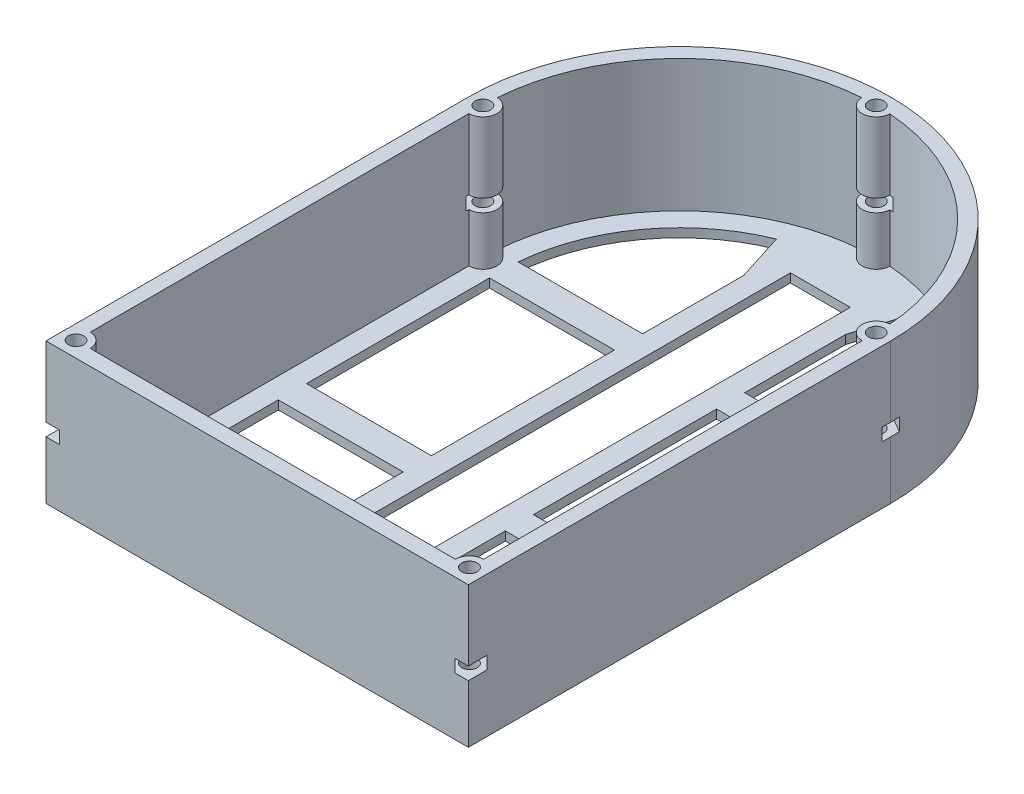
SolidWorks part; units mm, degrees
ref_plane "Front Plane" through (0, 0, 0) normal (0, 0, 1) x (1, 0, 0)
ref_plane "Top Plane" through (0, 0, 0) normal (0, 1, 0) x (1, 0, 0)
ref_plane "Right Plane" through (0, 0, 0) normal (1, 0, 0) x (0, 0, -1)
sketch "Sketch1" plane through (0, 0, 0) normal (0, 1, 0) x (1, 0, 0)
  line L1 (-30, 0) -> (30, 0) construction
  line L2 (-30, 0) -> (-30, -60)
  line L3 (-30, -60) -> (30, -60)
  line L4 (30, 0) -> (30, -60)
  line L5 (-30, 0) -> (30, -60) construction
  line L6 (-30, -60) -> (30, 0) construction
  line L9 (27.785, -57.785) -> (27.94, -57.785)
  line L10 (27.94, -55.785) -> (27.94, -2)
  line L11 (-25.94, -57.785) -> (25.94, -57.785)
  line L12 (-27.94, -2) -> (-27.94, -55.785)
  arc A0 (-30, 0) -> (30, 0) centre (0, 0) cw
  circle A1 centre (27.94, 0) radius 1.1
  circle A2 centre (-27.94, 0) radius 1.1
  circle A3 centre (0, 27.94) radius 1.1
  circle A4 centre (-27.94, -57.785) radius 1.1
  circle A5 centre (27.94, -57.785) radius 1.1
  arc A7 (27.8684, 1.9987) -> (27.94, -2) centre (27.94, 0) ccw
  arc A8 (27.94, -55.785) -> (25.94, -57.785) centre (27.94, -57.785) ccw
  arc A9 (-25.94, -57.785) -> (-27.94, -55.785) centre (-27.94, -57.785) ccw
  arc A11 (-1.9987, 27.8684) -> (1.9987, 27.8684) centre (0, 27.94) ccw
  circle A12 centre (0, 27.94) radius 2 construction
  circle A13 centre (27.94, 0) radius 2 construction
  arc A14 (1.9987, 27.8684) -> (27.8684, 1.9987) centre (0, 0) cw
  arc A15 (29.9391, -0.0609) -> (29.94, 0) centre (27.94, 0) ccw
  circle A16 centre (27.94, -57.785) radius 2 construction
  circle A17 centre (-27.94, -57.785) radius 2 construction
  arc A18 (-27.8684, 1.9987) -> (-1.9987, 27.8684) centre (0, 0) cw
  arc A19 (-27.94, -2) -> (-27.8684, 1.9987) centre (-27.94, 0) ccw
  point P0 (0, -30)
  dimension "D3" = 27.94
  dimension "D4" = 2.2
  dimension "D1" = 60
  dimension "D2" = 60
  dimension "D5" = 27.94
  dimension "D6" = 27.94
  dimension "D7" = 57.785
  dimension "D8" = 0.9
extrude "Boss-Extrude1" add sketch "Sketch1" against normal blind 20
sketch "Sketch2" plane through (0, -20, 0) normal (0, -1, 0) x (1, 0, 0)
  line L0 (-7.25, 53) -> (-7.25, 32)
  line L1 (-4.25, 50) -> (4.25, 50)
  line L2 (-4.25, 50) -> (-4.25, -20)
  line L3 (30, 0) -> (30, 60)
  line L4 (30, 60) -> (-30, 60)
  line L5 (-30, 60) -> (-30, 0)
  line L6 (30, 0) -> (30, 60)
  line L7 (30, 60) -> (-30, 60)
  line L8 (-30, 60) -> (-30, 0)
  line L9 (-4.25, -20) -> (4.25, -20)
  line L10 (4.25, 50) -> (4.25, -20)
  line L11 (-4.25, 50) -> (4.25, -20) construction
  line L12 (-4.25, -20) -> (4.25, 50) construction
  line L13 (-5.153, -23) -> (5.153, -23) construction
  line L14 (7.25, 53) -> (7.25, 32)
  line L16 (0, 0) -> (-7.5159, -23.8435) construction
  line L17 (25, 2) -> (25, 28)
  line L18 (0, 0) -> (7.5159, -23.8435) construction
  line L19 (25, 55) -> (7.25, 55)
  line L20 (-25, 55) -> (-25, 32)
  line L22 (-7.25, 53) -> (-7.25, 55)
  line L23 (5.153, -23) -> (5.5843, -24.3683) construction
  line L24 (-5.153, -23) -> (-5.5843, -24.3683) construction
  line L25 (-7.25, 53) -> (-7.25, -23) construction
  line L26 (-7.25, -23) -> (7.25, -23) construction
  line L27 (7.25, 53) -> (7.25, -23) construction
  line L28 (0, -6.6526) -> (-5.6084, -24.4448) construction
  line L29 (0, -6.6526) -> (5.6084, -24.4448) construction
  line L30 (-7.25, -16.3474) -> (-9.3993, -23.1658)
  line L31 (7.25, 53) -> (7.25, 55)
  line L32 (7.25, -16.3474) -> (9.3993, -23.1658)
  line L34 (-7.25, 55) -> (-25, 55)
  line L35 (25, 55) -> (-25, 55) construction
  line L36 (-7.25, 53) -> (7.25, 53) construction
  line L37 (-25, 0) -> (-7.25, 0) construction
  line L38 (25, 0) -> (7.25, 0) construction
  line L39 (7.25, 30) -> (25, 30) construction
  line L40 (-7.25, 30) -> (-25, 30) construction
  line L41 (-24.9199, -2) -> (-7.25, -2)
  line L42 (25, 2) -> (7.25, 2)
  line L43 (-7.25, 32) -> (-25, 32)
  line L44 (7.25, 28) -> (25, 28)
  line L45 (-25, 2) -> (-7.25, 2)
  line L46 (24.9199, -2) -> (7.25, -2)
  line L47 (-7.25, 28) -> (-25, 28)
  line L48 (7.25, 32) -> (25, 32)
  line L49 (7.25, 2) -> (7.25, 0) construction
  line L50 (7.25, -2) -> (7.25, -16.3474)
  line L51 (7.25, 0) -> (7.25, -2) construction
  line L52 (-7.25, 0) -> (-7.25, -2) construction
  line L53 (-7.25, -2) -> (-7.25, -16.3474)
  line L54 (-7.25, 2) -> (-7.25, 0) construction
  line L55 (-7.25, 32) -> (-7.25, 30) construction
  line L56 (-7.25, 28) -> (-7.25, 2)
  line L57 (-7.25, 30) -> (-7.25, 28) construction
  line L58 (7.25, 32) -> (7.25, 30) construction
  line L59 (7.25, 28) -> (7.25, 2)
  line L60 (7.25, 30) -> (7.25, 28) construction
  line L61 (-25, 32) -> (-25, 30) construction
  line L62 (-25, 28) -> (-25, 2)
  line L63 (-25, 55) -> (-25, 0) construction
  line L64 (-25, 30) -> (-25, 28) construction
  line L65 (25, 30) -> (25, 32) construction
  line L66 (25, 32) -> (25, 55)
  line L67 (25, 0) -> (25, 55) construction
  line L68 (25, 28) -> (25, 30) construction
  line L69 (25, 0) -> (25, 2) construction
  line L70 (-25, 2) -> (-25, 0) construction
  line L71 (9.3993, -23.1658) -> (9.4234, -23.2422) construction
  line L72 (-9.3993, -23.1658) -> (-9.4234, -23.2422) construction
  line L73 (-25, -2) -> (-24.9199, -2) construction
  line L74 (-25, -2) -> (-7.25, -2) construction
  line L75 (25, -2) -> (24.9199, -2) construction
  line L76 (25, -2) -> (7.25, -2) construction
  arc A0 (-24.9199, -2) -> (-9.3993, -23.1658) centre (0, 0) ccw
  arc A1 (-30, 0) -> (30, 0) centre (0, 0) ccw
  arc A2 (-30, 0) -> (30, 0) centre (0, 0) ccw
  arc A3 (-5.5843, -24.3683) -> (5.5843, -24.3683) centre (0, 0) ccw construction
  arc A4 (-25, 0) -> (25, 0) centre (0, 0) ccw construction
  arc A5 (9.3993, -23.1658) -> (24.9199, -2) centre (0, 0) ccw
  arc A6 (24.9199, -2) -> (25, 0) centre (0, 0) ccw construction
  arc A7 (-25, 0) -> (-24.9199, -2) centre (0, 0) ccw construction
  point P0 (0, 15)
  dimension "D2" = 8.5
  dimension "D3" = 70
  dimension "D4" = 15
  dimension "D7" = 30
  dimension "D1" = 0
  dimension "D5" = 3
  dimension "D6" = 5
  dimension "D8" = 2
  dimension "D9" = 2
  dimension "D10" = 2
extrude "Boss-Extrude2" add sketch "Sketch2" against normal blind 1.25
sketch "Sketch3" plane through (0, 0, 0) normal (0, 1, 0) x (1, 0, 0)
  line L0 (-30, -60) -> (30, -60) construction
  line L1 (2.4249, 27.94) -> (1.2124, 30.04)
  line L2 (1.2124, 30.04) -> (-1.2124, 30.04)
  line L3 (-1.2124, 30.04) -> (-2.4249, 27.94)
  line L4 (-1.8187, 26.89) -> (-1.2124, 25.84) construction
  line L5 (-1.2124, 25.84) -> (1.2124, 25.84)
  line L6 (1.8187, 26.89) -> (2.4249, 27.94) construction
  line L7 (27.94, -2.4249) -> (30.04, -1.2124)
  line L8 (30.04, -1.2124) -> (30.04, 1.2124)
  line L9 (30.04, 1.2124) -> (27.94, 2.4249)
  line L10 (26.89, 1.8187) -> (25.84, 1.2124) construction
  line L11 (25.84, 1.2124) -> (25.84, -1.2124)
  line L12 (25.84, -1.2124) -> (27.94, -2.4249)
  line L13 (30.2822, -58.4126) -> (29.6546, -56.0704)
  line L14 (29.6546, -56.0704) -> (27.3124, -55.4428)
  line L15 (27.3124, -55.4428) -> (25.5978, -57.1574)
  line L16 (25.5978, -57.1574) -> (26.2254, -59.4996)
  line L17 (26.2254, -59.4996) -> (28.5676, -60.1272)
  line L18 (29.4249, -59.2699) -> (30.2822, -58.4126) construction
  line L19 (-25.5978, -57.1574) -> (-27.3124, -55.4428)
  line L20 (-27.3124, -55.4428) -> (-29.6546, -56.0704)
  line L21 (-29.6546, -56.0704) -> (-30.2822, -58.4126)
  line L22 (-29.4249, -59.2699) -> (-28.5676, -60.1272) construction
  line L23 (-28.5676, -60.1272) -> (-26.2254, -59.4996)
  line L24 (-26.2254, -59.4996) -> (-25.5978, -57.1574)
  line L25 (-30.04, 1.2124) -> (-30.04, -1.2124)
  line L26 (-30.04, -1.2124) -> (-27.94, -2.4249)
  line L27 (-27.94, -2.4249) -> (-25.84, -1.2124)
  line L28 (-25.84, -1.2124) -> (-25.84, 1.2124)
  line L29 (-25.84, 1.2124) -> (-26.89, 1.8187) construction
  line L30 (-27.94, 2.4249) -> (-30.04, 1.2124)
  line L31 (-30.2822, -58.4126) -> (-30.9098, -60.7548)
  line L32 (-30.9098, -60.7548) -> (-28.5676, -60.1272)
  line L33 (-30.2822, -58.4126) -> (-29.4249, -59.2699) construction
  line L34 (28.5676, -60.1272) -> (30.9098, -60.7548)
  line L35 (30.9098, -60.7548) -> (30.2822, -58.4126)
  line L36 (28.5676, -60.1272) -> (29.4249, -59.2699) construction
  line L37 (-27.94, 2.4249) -> (-27.4431, 2.7117)
  line L38 (-27.4431, 2.7117) -> (-25.84, 1.2124)
  line L39 (-26.89, 1.8187) -> (-27.94, 2.4249) construction
  line L40 (27.94, 2.4249) -> (27.2976, 2.7958)
  line L41 (27.2976, 2.7958) -> (25.84, 1.2124)
  line L42 (27.94, 2.4249) -> (26.89, 1.8187) construction
  line L43 (-2.4249, 27.94) -> (-2.9234, 27.0765)
  line L44 (-2.9234, 27.0765) -> (-1.2124, 25.84)
  line L45 (1.2124, 25.84) -> (2.6648, 27.5244)
  line L46 (2.6648, 27.5244) -> (2.4249, 27.94)
  line L47 (-2.4249, 27.94) -> (-1.8187, 26.89) construction
  line L48 (1.2124, 25.84) -> (1.8187, 26.89) construction
  circle A0 centre (0, 27.94) radius 2.1 construction
  circle A1 centre (27.94, 0) radius 2.1 construction
  circle A2 centre (27.94, -57.785) radius 2.1 construction
  circle A3 centre (-27.94, -57.785) radius 2.1 construction
  circle A4 centre (-27.94, 0) radius 2.1 construction
  dimension "D1" = 4.2
  dimension "D2" = 45
  dimension "D3" = 45
extrude "Cut-Extrude1" cut sketch "Sketch3" against normal blind 1.8 from offset 10 offset against normal yes
